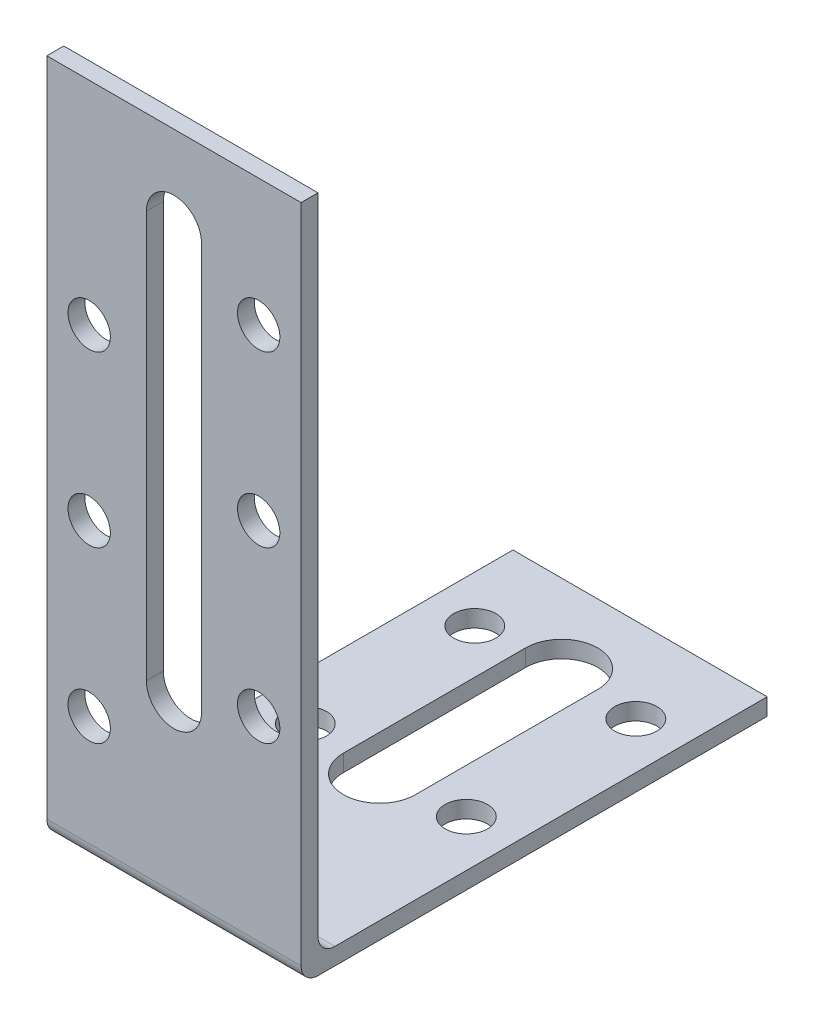
SolidWorks part; units mm, degrees
ref_plane "Plan de face" through (0, 0, 0) normal (0, 0, 1) x (1, 0, 0)
ref_plane "Plan de dessus" through (0, 0, 0) normal (0, 1, 0) x (1, 0, 0)
ref_plane "Plan de droite" through (0, 0, 0) normal (1, 0, 0) x (0, 0, -1)
sketch "Esquisse1" plane through (0, 0, 0) normal (1, 0, 0) x (0, 0, -1)
  line L0 (0, 0) -> (0, 80)
  line L1 (0, 80) -> (2, 80)
  line L2 (2, 80) -> (2, 2)
  line L3 (2, 2) -> (55, 2)
  line L4 (55, 2) -> (55, 0)
  line L5 (55, 0) -> (0, 0)
  dimension "D1" = 2
  dimension "D2" = 2
  dimension "D3" = 80
  dimension "D4" = 55
extrude "Boss.-Extru.1" add sketch "Esquisse1" along normal mid plane 30
fillet "Congé1" radius 2 2 edges at (0, 0, 0) (0, 2, -2)
sketch "Esquisse2" plane through (0, 2, 0) normal (0, 1, 0) x (1, 0, 0)
  line L0 (0, 24.25) -> (0, 45.75) construction
  line L1 (-4.25, 24.25) -> (-4.25, 45.75)
  line L2 (4.25, 24.25) -> (4.25, 45.75)
  line L4 (15, 55) -> (-15, 55) construction
  line L5 (15, 55) -> (15, 4) construction
  line L6 (-15, 35) -> (15, 35) construction
  line L8 (-15, 55) -> (-15, 4) construction
  line L9 (0, 55) -> (0, 2) construction
  line L10 (15, 2) -> (-15, 2) construction
  arc A0 (-4.25, 24.25) -> (4.25, 24.25) centre (0, 24.25) ccw
  arc A1 (4.25, 45.75) -> (-4.25, 45.75) centre (0, 45.75) ccw
  circle A2 centre (9.5, 45) radius 2.5
  circle A3 centre (9.5, 25) radius 2.5
  circle A4 centre (9.5, 45) radius 2.5
  circle A5 centre (9.5, 25) radius 2.5
  circle A6 centre (-9.5, 45) radius 2.5
  circle A7 centre (-9.5, 25) radius 2.5
  point P3 (0, 35)
  dimension "D1" = 4.25
  dimension "D6" = 5
  dimension "D2" = 21.5
  dimension "D3" = 9.25
  dimension "D4" = 10
  dimension "D5" = 5.5
extrude "Enlèv. mat.-Extru.1" cut sketch "Esquisse2" against normal up to next contours L2 A1 L1 A0 | A7 | A6 | A2 | A3
sketch "Esquisse4" plane through (0, 0, -2) normal (0, 0, -1) x (-1, 0, 0)
  line L0 (0, 70) -> (0, 22) construction
  line L1 (3.25, 70) -> (3.25, 22)
  line L2 (-3.25, 70) -> (-3.25, 22)
  line L3 (-15, 80) -> (15, 80) construction
  line L5 (15, 4) -> (15, 80) construction
  arc A0 (3.25, 70) -> (-3.25, 70) centre (0, 70) ccw
  arc A1 (-3.25, 22) -> (3.25, 22) centre (0, 22) ccw
  circle A2 centre (-10, 65) radius 2.5
  circle A3 centre (-10, 45) radius 2.5
  circle A4 centre (-10, 25) radius 2.5
  circle A5 centre (10, 55) radius 2.5
  circle A6 centre (10, 35) radius 2.5
  circle A7 centre (10, 15) radius 2.5
  point P3 (0, 46)
  dimension "D1" = 3.25
  dimension "D5" = 5
  dimension "D9" = 5
  dimension "D11" = 25
  dimension "D13" = 20
  dimension "D2" = 48
  dimension "D3" = 10
  dimension "D4" = 10
  dimension "D6" = 15
  dimension "D8" = 20
  dimension "D10" = 5
  dimension "D7" = 3
  dimension "D12" = 3
extrude "Enlèv. mat.-Extru.2" cut sketch "Esquisse4" against normal up to next
